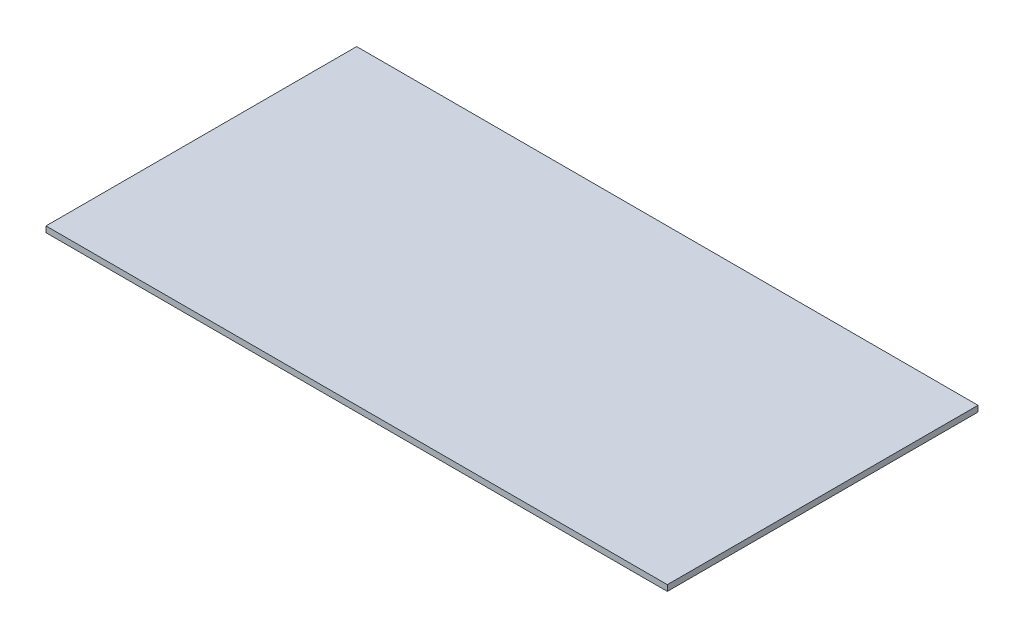
SolidWorks part; units mm, degrees
ref_plane "Front Plane" through (0, 0, 0) normal (0, 0, 1) x (1, 0, 0)
ref_plane "Top Plane" through (0, 0, 0) normal (0, 1, 0) x (1, 0, 0)
ref_plane "Right Plane" through (0, 0, 0) normal (1, 0, 0) x (0, 0, -1)
sketch "Sketch1" plane through (0, 0, 0) normal (0, 1, 0) x (1, 0, 0)
  line L1 (0, 0) -> (501.65, 0)
  line L2 (0, 0) -> (0, -250.825)
  line L3 (0, -250.825) -> (501.65, -250.825)
  line L4 (501.65, 0) -> (501.65, -250.825)
  dimension "D1" = 250.825
  dimension "D2" = 501.65
extrude "Boss-Extrude1" add sketch "Sketch1" along normal blind 4.7625 contours L1 L4 L3 L2
